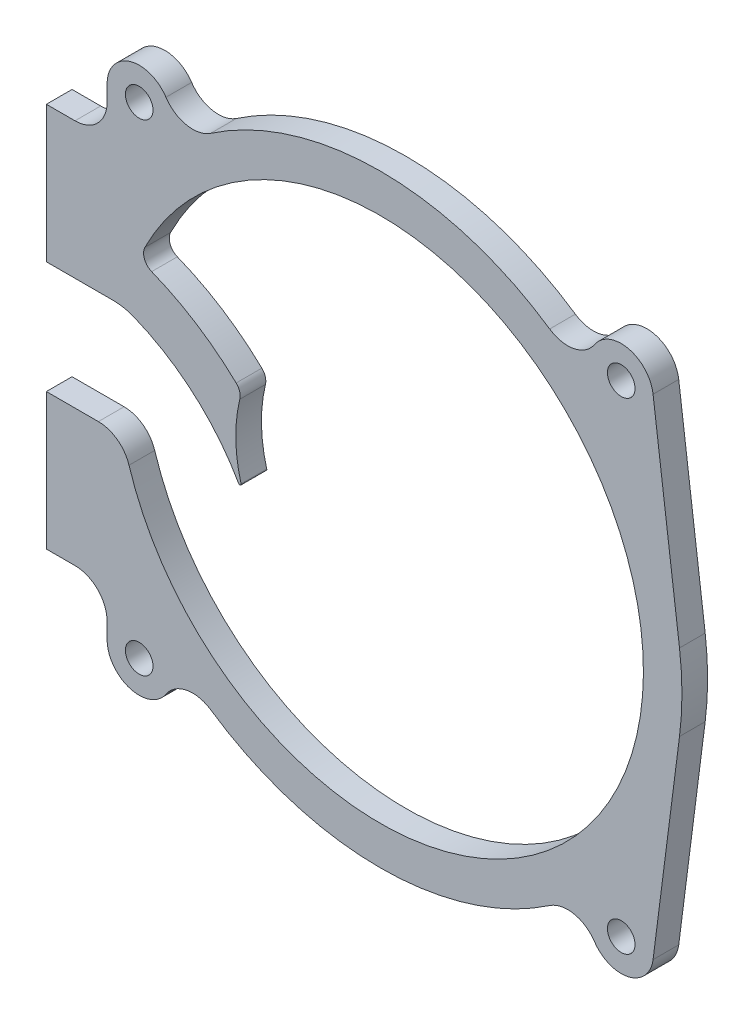
SolidWorks part; units mm, degrees
material "Thornel Mat VMA"
ref_plane "前视基准面" through (0, 0, 0) normal (0, 0, 1) x (1, 0, 0)
ref_plane "上视基准面" through (0, 0, 0) normal (0, 1, 0) x (1, 0, 0)
ref_plane "右视基准面" through (0, 0, 0) normal (1, 0, 0) x (0, 0, -1)
sketch "草图1" plane through (0, 0, 0) normal (0, 0, 1) x (1, 0, 0)
  line L0 (0, 0) -> (50000, 0) construction
  line L1 (-52, 8.75) -> (-52, -8.75) construction
  line L2 (-52, 8.75) -> (-52, 30)
  line L3 (-52, -8.75) -> (-52, -30)
  line L4 (-52, 8.75) -> (-40.0554, 8.75)
  line L5 (-52, -8.75) -> (-40.0554, -8.75)
  line L6 (-42.54, 37.5) -> (-42.54, 35)
  line L7 (-47.54, 30) -> (-52, 30)
  line L8 (-47.54, -30) -> (-52, -30)
  line L9 (-42.54, -37.5) -> (-42.54, -35)
  line L10 (0, 0) -> (0, -50000) construction
  line L11 (42.4995, 38.1352) -> (46.6192, 5.9711)
  line L12 (42.4995, -38.1352) -> (46.6192, -5.9711)
  arc A0 (-40.0554, -8.75) -> (-37.5934, 16.3627) centre (0, 0) ccw
  arc A1 (-40.0554, 8.75) -> (-40.0554, -8.75) centre (0, 0) ccw construction
  circle A2 centre (-37.54, 37.5) radius 2.15
  circle A3 centre (-37.54, -37.5) radius 2.15
  arc A4 (-33.3722, 40.2622) -> (-42.54, 37.5) centre (-37.54, 37.5) ccw
  arc A5 (-42.54, -37.5) -> (-33.3722, -40.2622) centre (-37.54, -37.5) ccw
  arc A6 (-26.3963, -38.8874) -> (26.3963, -38.8874) centre (0, 0) ccw
  arc A7 (-33.3722, 40.2622) -> (-26.3963, 38.8874) centre (-29.2045, 43.0244) ccw
  arc A8 (-33.3722, -40.2622) -> (-42.54, -37.5) centre (-37.54, -37.5) cw
  arc A9 (-33.3722, -40.2622) -> (-26.3963, -38.8874) centre (-29.2045, -43.0244) cw
  circle A10 centre (37.54, -37.5) radius 2.15
  circle A11 centre (37.54, 37.5) radius 2.15
  arc A12 (42.4995, 38.1352) -> (33.3722, 40.2622) centre (37.54, 37.5) ccw
  arc A13 (33.3722, -40.2622) -> (42.4995, -38.1352) centre (37.54, -37.5) ccw
  arc A14 (33.3722, 40.2622) -> (26.3963, 38.8874) centre (29.2045, 43.0244) cw
  arc A15 (33.3722, -40.2622) -> (26.3963, -38.8874) centre (29.2045, -43.0244) ccw
  arc A16 (26.3963, 38.8874) -> (-26.3963, 38.8874) centre (0, 0) ccw
  arc A17 (46.6192, -5.9711) -> (46.6192, 5.9711) centre (0, 0) ccw
  arc A18 (-47.54, -30) -> (-42.54, -35) centre (-47.54, -35) cw
  arc A19 (-42.54, 35) -> (-47.54, 30) centre (-47.54, 35) cw
  circle A20 centre (0, 0) radius 22.5 construction
  arc A21 (-40.0554, 8.75) -> (-20.5735, -9.1093) centre (-50.748, -22.4697) cw
  arc A22 (-20.5735, -9.1093) -> (-21.5855, 6.3495) centre (0, 0) cw
  arc A23 (-37.5934, 16.3627) -> (-21.5855, 6.3495) centre (-50.748, -22.4697) cw
  point P8 (-52, 0)
  point P44 (-42.54, -30)
  point P47 (-42.54, 30)
  dimension "D1" = 82
  dimension "D5" = 4.3
  dimension "D6" = 75
  dimension "D8" = 10
  dimension "D9" = 94
  dimension "D10" = 5
  dimension "D11" = 10
  dimension "D12" = 5
  dimension "D13" = 5
  dimension "D14" = 5
  dimension "D15" = 45
  dimension "D16" = 33
  dimension "D17" = 41
  dimension "D2" = 17.5
  dimension "D3" = 52
  dimension "D4" = 60
  dimension "D7" = 14.46
extrude "凸台-拉伸1" add sketch "草图1" along normal blind 4
fillet "圆角1" radius 0.2 1 edges at (-20.5735, -9.1093, 2)
fillet "圆角2" radius 2 1 edges at (-21.5855, 6.3495, 2)
fillet "圆角3" radius 2 1 edges at (-37.5934, 16.3627, 2)
fillet "圆角4" radius 8.5 1 edges at (-40.0554, 8.75, 2)
fillet "圆角5" radius 5 1 edges at (-40.0554, -8.75, 2)
